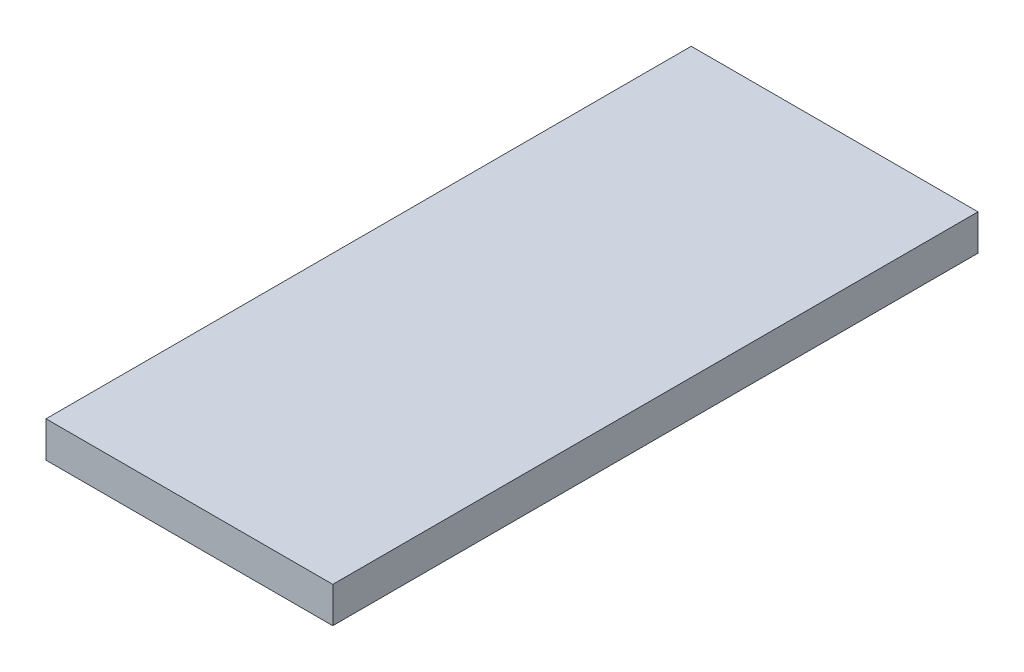
SolidWorks part; units mm, degrees
ref_plane "Front Plane" through (0, 0, 0) normal (0, 0, 1) x (1, 0, 0)
ref_plane "Top Plane" through (0, 0, 0) normal (0, 1, 0) x (1, 0, 0)
ref_plane "Right Plane" through (0, 0, 0) normal (1, 0, 0) x (0, 0, -1)
sketch "Sketch1" plane through (0, 0, 0) normal (1, 0, 0) x (0, 0, -1)
  line L9 (-2.9074, 3.2037) -> (87.0926, 3.2037)
  line L10 (-2.9074, 3.2037) -> (-2.9074, -1.7963)
  line L11 (-2.9074, -1.7963) -> (87.0926, -1.7963)
  line L12 (87.0926, 3.2037) -> (87.0926, -1.7963)
  dimension "D1" = 5
  dimension "D2" = 90
extrude "Boss-Extrude1" add sketch "Sketch1" along normal blind 40
